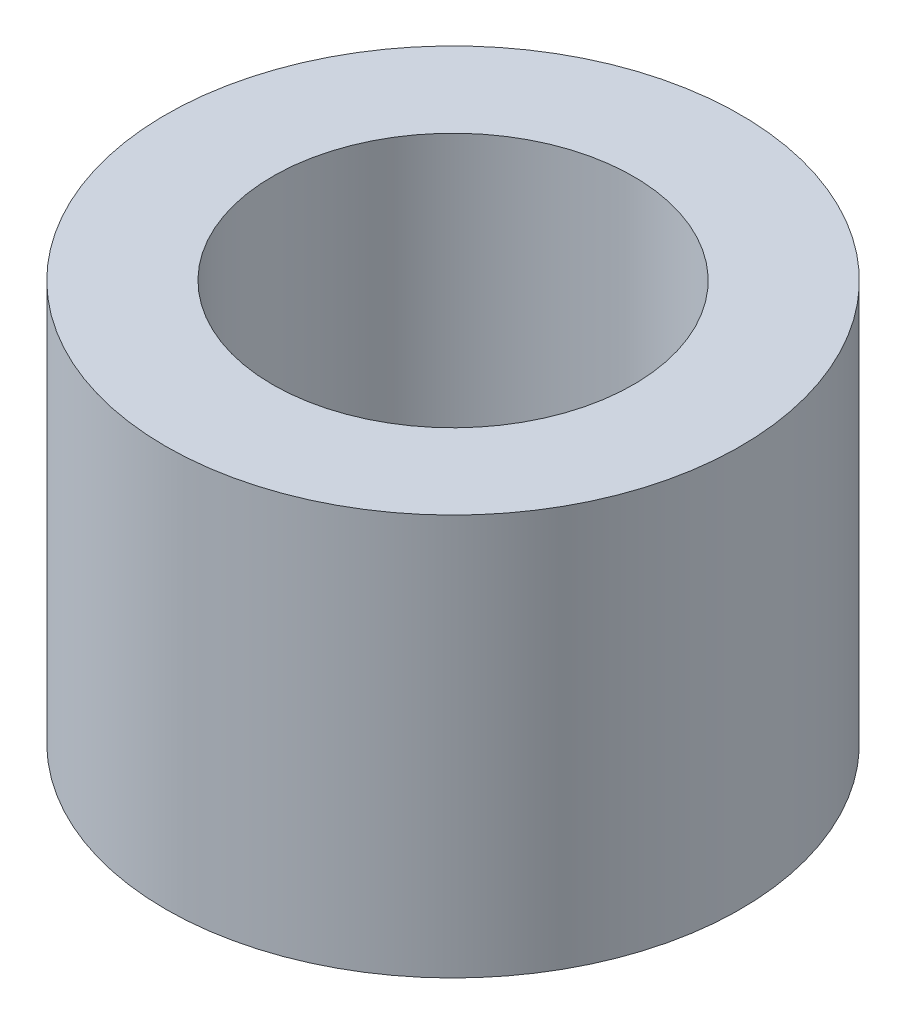
SolidWorks part; units mm, degrees
material "Ti-6Al-2Sn-2Zr-2Mo-2Cr-0.25Si (SS)"
ref_plane "Front Plane" through (0, 0, 0) normal (0, 0, 1) x (1, 0, 0)
ref_plane "Top Plane" through (0, 0, 0) normal (0, 1, 0) x (1, 0, 0)
ref_plane "Right Plane" through (0, 0, 0) normal (1, 0, 0) x (0, 0, -1)
sketch "Sketch1" plane through (0, 0, 0) normal (0, 1, 0) x (1, 0, 0)
  circle A0 centre (0, 0) radius 107.5
  dimension "D1" = 215
extrude "Boss-Extrude1" add sketch "Sketch1" along normal blind 150
sketch "Sketch2" plane through (0, 150, 0) normal (0, 1, 0) x (1, 0, 0)
  circle A0 centre (0, 0) radius 107.5
  circle A1 centre (0, 0) radius 67.5
  dimension "D1" = 135
extrude "Cut-Extrude1" cut sketch "Sketch2" against normal through all contours A1
